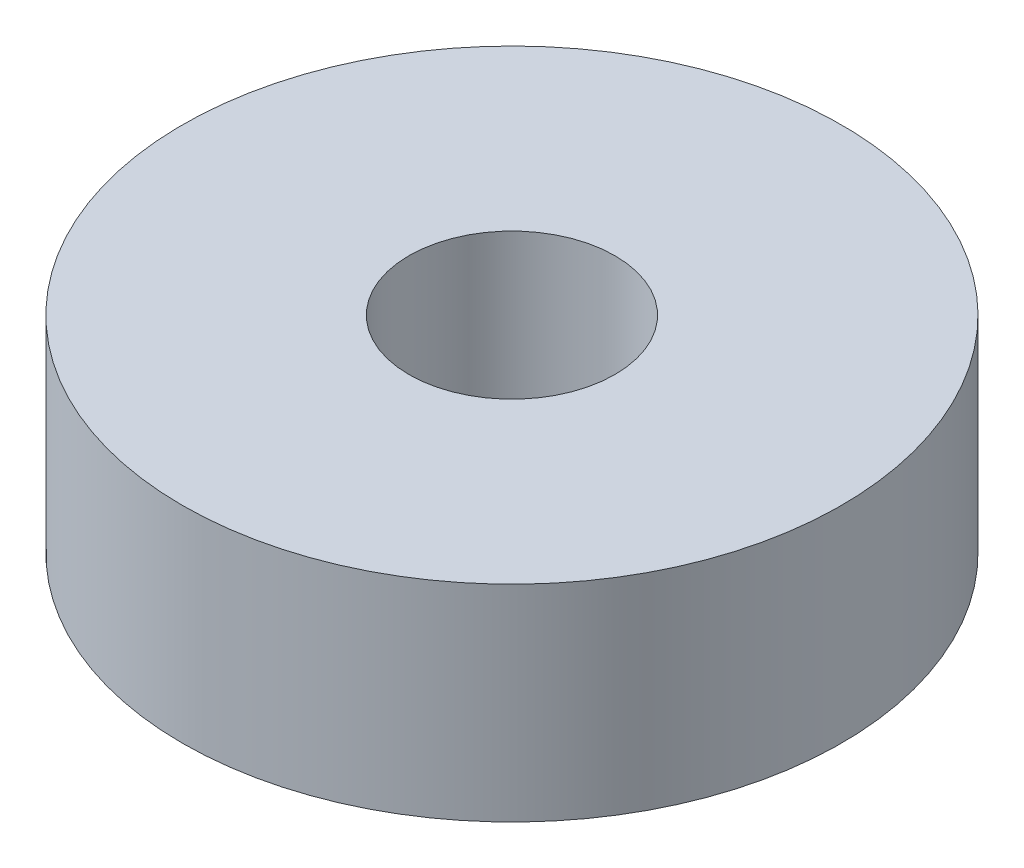
SolidWorks part; units mm, degrees
ref_plane "Front Plane" through (0, 0, 0) normal (0, 0, 1) x (1, 0, 0)
ref_plane "Top Plane" through (0, 0, 0) normal (0, 1, 0) x (1, 0, 0)
ref_plane "Right Plane" through (0, 0, 0) normal (1, 0, 0) x (0, 0, -1)
sketch "Sketch1" plane through (0, 0, 0) normal (0, 1, 0) x (1, 0, 0)
  circle A0 centre (0, 0) radius 2.5
  circle A1 centre (0, 0) radius 8
  dimension "D1" = 16
  dimension "D2" = 5
extrude "Boss-Extrude1" add sketch "Sketch1" along normal blind 5
